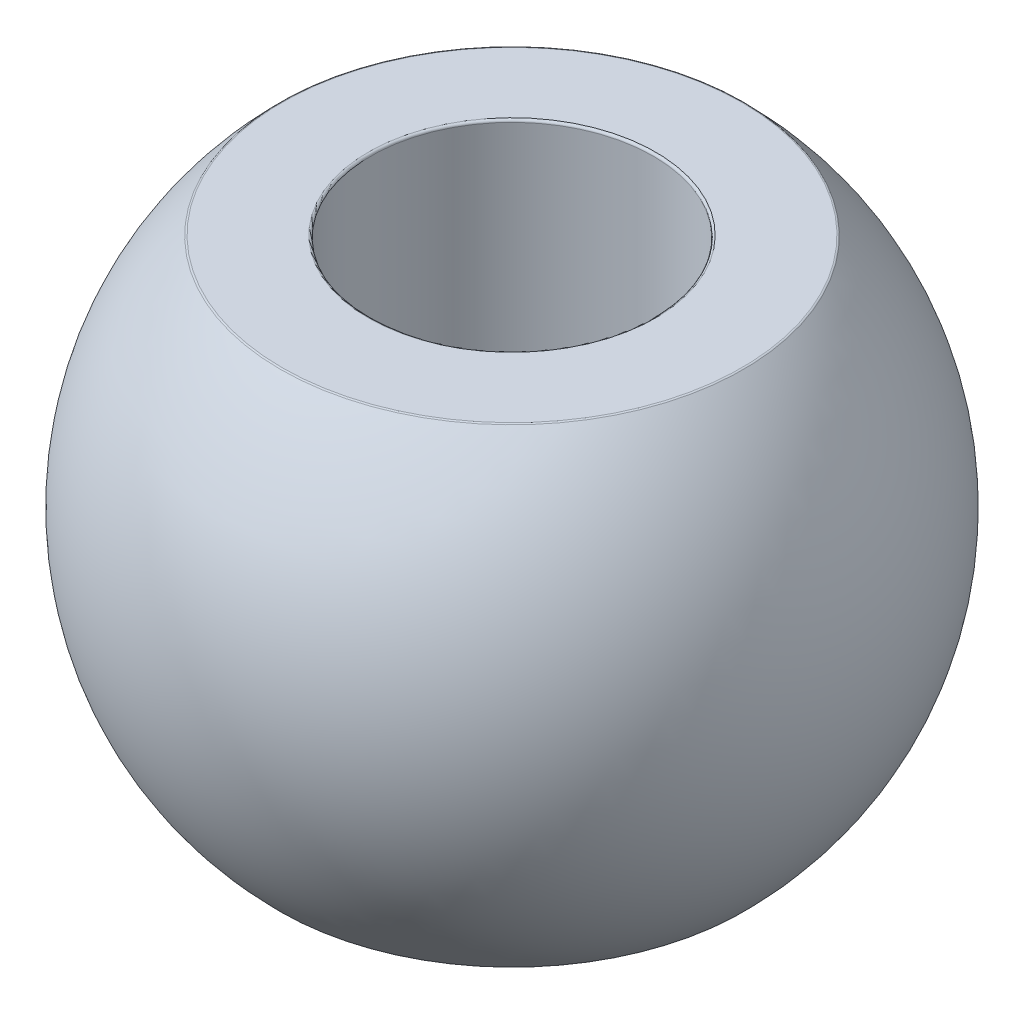
SolidWorks part; units mm, degrees
ref_plane "Front Plane" through (0, 0, 0) normal (0, 0, 1) x (1, 0, 0)
ref_plane "Top Plane" through (0, 0, 0) normal (0, 1, 0) x (1, 0, 0)
ref_plane "Right Plane" through (0, 0, 0) normal (1, 0, 0) x (0, 0, -1)
sketch "Sketch1" plane through (0, 0, 0) normal (0, 0, 1) x (1, 0, 0)
  line L0 (6, 0) -> (0, 0) construction
  line L1 (0, 0) -> (0, 12.58) construction
  line L2 (6, -10) -> (6, 10)
  line L3 (6, 10) -> (9.798, 10)
  line L4 (6, -10) -> (9.798, -10)
  arc A0 (9.798, 10) -> (9.798, -10) centre (0, 0) cw
  dimension "D3" = 14
  dimension "D1" = 6
  dimension "D2" = 20
revolve "Revolve1" add sketch "Sketch1" angle 360 about L1
fillet "Fillet1" radius 0.1 4 edges at (0, -10, -9.798) (0, 10, -9.798) (0, 10, -6) (0, -10, -6)
